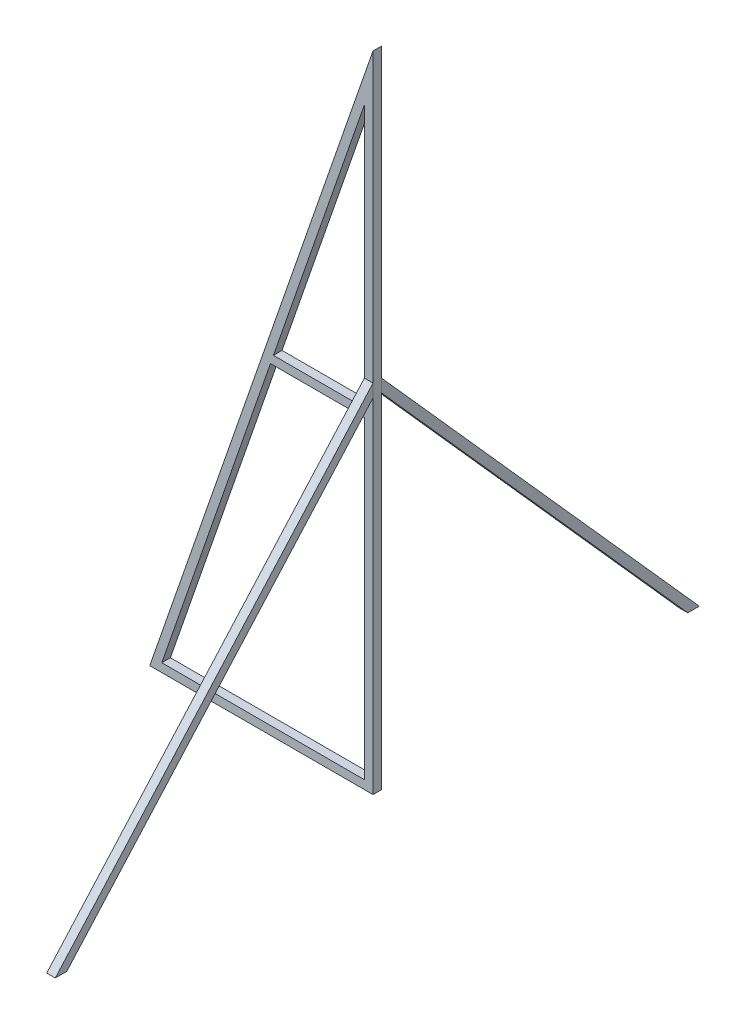
SolidWorks part; units mm, degrees
material "ﾊﾞﾙｻ"
ref_plane "正面" through (0, 0, 0) normal (0, 0, 1) x (1, 0, 0)
ref_plane "平面" through (0, 0, 0) normal (0, 1, 0) x (1, 0, 0)
ref_plane "右側面" through (0, 0, 0) normal (1, 0, 0) x (0, 0, -1)
sketch "ｽｹｯﾁ1" plane through (0, 0, 0) normal (0, 0, 1) x (1, 0, 0)
  line L0 (0, 0) -> (52, 0)
  line L1 (52, 0) -> (52, 150)
  line L2 (52, 150) -> (0, 0)
  line L3 (50, 138.1247) -> (2.8101, 2)
  line L4 (2.8101, 2) -> (50, 2)
  line L5 (50, 2) -> (50, 138.1247)
  line L6 (28.8101, 77) -> (50, 77)
  line L7 (28.1168, 75) -> (50, 75)
  point P11 (39.4051, 77)
  dimension "D1" = 52
  dimension "D2" = 150
  dimension "D4" = 2
  dimension "D5" = 75
  dimension "D3" = 2
extrude "ﾎﾞｽ - 押し出し1" add sketch "ｽｹｯﾁ1" along normal blind 2 contours L1 L2 L0 L5 L4 L3 | L3 L7 L5 L6
sketch "ｽｹｯﾁ2" plane through (52, 0, 0) normal (1, 0, 0) x (0, 0, -1)
  line L0 (-2, 83.0055) -> (-76, 0)
  line L1 (-2, 0) -> (-2, 150) construction
  line L2 (-76, 0) -> (-73.3206, 0)
  line L3 (-73.3206, 0) -> (-2, 80)
  line L4 (-2, 80) -> (-2, 83.0055)
  line L5 (-1, 0) -> (-1, 8.6037) construction
  line L6 (-2, 0) -> (0, 0) construction
  line L7 (74, 0) -> (71.3206, 0)
  line L8 (0, 83.0055) -> (74, 0)
  line L9 (0, 80) -> (0, 83.0055)
  line L10 (71.3206, 0) -> (0, 80)
  dimension "D1" = 2
  dimension "D2" = 80
  dimension "D3" = 75
extrude "ﾎﾞｽ - 押し出し2" add sketch "ｽｹｯﾁ2" against normal blind 2 separate body
